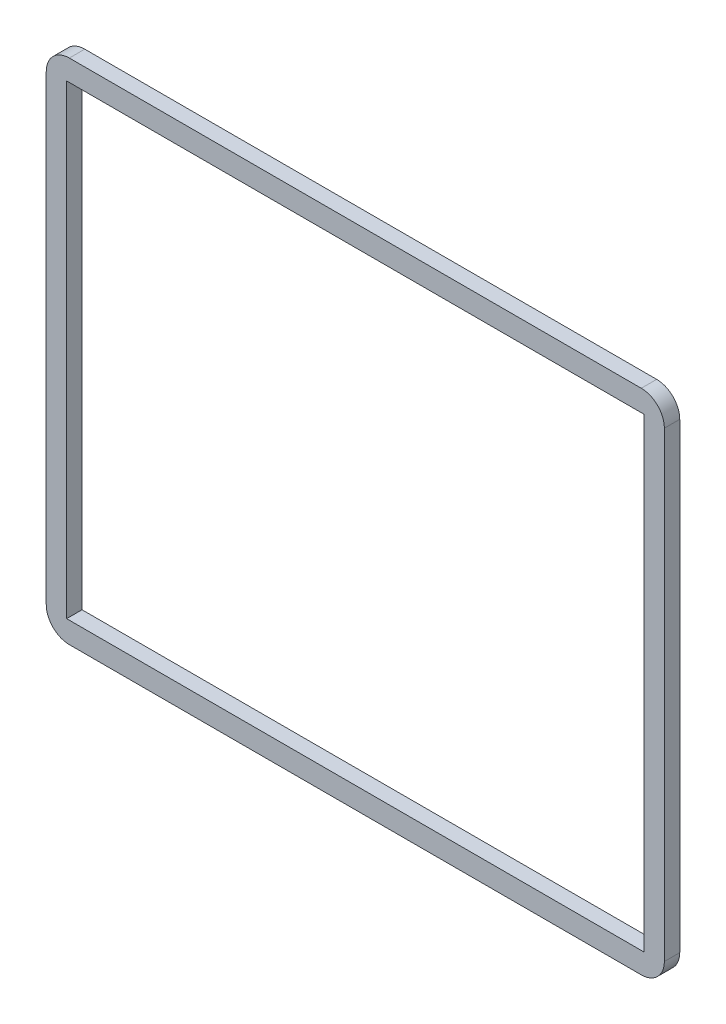
SolidWorks part; units mm, degrees
material "Acrylic (Medium-high impact)"
ref_plane "Front Plane" through (0, 0, 0) normal (0, 0, 1) x (1, 0, 0)
ref_plane "Top Plane" through (0, 0, 0) normal (0, 1, 0) x (1, 0, 0)
ref_plane "Right Plane" through (0, 0, 0) normal (1, 0, 0) x (0, 0, -1)
sketch "Sketch1" plane through (0, 0, 0) normal (0, 0, 1) x (1, 0, 0)
  line L1 (0, 0) -> (80.3, 0)
  line L2 (0, 0) -> (0, 66)
  line L3 (0, 66) -> (80.3, 66)
  line L4 (80.3, 0) -> (80.3, 66)
  dimension "D1" = 80.3
  dimension "D2" = 66
extrude "Boss-Extrude1" add sketch "Sketch1" along normal blind 2
hole_wizard "Ø3.2 (3.2) Diameter Hole1" positions "Sketch3" profile "Sketch2" hole size "Ø3.2" standard "ANSI Metric" end condition through all
sketch "Sketch3" plane through (0, 0, 2) normal (0, 0, 1) x (1, 0, 0)
  line L0 (0, 33) -> (80.3, 33) construction
  line L1 (0, 66) -> (0, 0) construction
  line L2 (80.3, 0) -> (80.3, 66) construction
  line L4 (7, 7) -> (7, 59) construction
  line L6 (7, 59) -> (73.3, 59) construction
  line L7 (73.3, 59) -> (73.3, 7) construction
  line L8 (73.3, 7) -> (7, 7) construction
  line L10 (40.15, 66) -> (40.15, 0) construction
  line L11 (80.3, 66) -> (0, 66) construction
  line L12 (0, 0) -> (80.3, 0) construction
  point P0 (7, 59)
  point P2 (73.3, 59)
  point P4 (73.3, 7)
  point P6 (7, 7)
  dimension "D1" = 66.3
  dimension "D2" = 52
  dimension "D3" = 26
  dimension "D4" = 33.15
sketch "Sketch2" plane through (7, 59, 2) normal (1, 0, 0) x (0, -1, 0)
  line L0 (0, 0) -> (0, 2)
  line L1 (0, 2) -> (1.6, 2)
  line L2 (1.6, 2) -> (1.6, 0)
  line L5 (1.6, 0) -> (0, 0)
  line L11 (0, -6.35) -> (0, 107.95) construction
  dimension "Thru Hole Dia." = 3.2
  dimension "Thru Hole Depth" = 2
fillet "Fillet1" radius 3 4 edges at (80.3, 66, 1) (80.3, 0, 1) (0, 0, 1) (0, 66, 1)
sketch "Sketch4" plane through (0, 0, 2) normal (0, 0, 1) x (1, 0, 0)
  line L0 (7, 59) -> (7, 7) construction
  line L1 (2.65, 2.75) -> (77.65, 2.75)
  line L2 (2.65, 2.75) -> (2.65, 63.25)
  line L3 (2.65, 63.25) -> (77.65, 63.25)
  line L4 (77.65, 2.75) -> (77.65, 63.25)
  line L5 (2.65, 33) -> (77.65, 33) construction
  line L6 (7, 59) -> (73.3, 59) construction
  line L7 (73.3, 59) -> (73.3, 7) construction
  line L8 (73.3, 7) -> (7, 7) construction
  line L9 (7, 33) -> (73.3, 33) construction
  line L10 (40.15, 59) -> (40.15, 7) construction
  line L11 (40.15, 63.25) -> (40.15, 2.75) construction
  dimension "D1" = 75
  dimension "D2" = 60.5
extrude "Cut-Extrude1" cut sketch "Sketch4" against normal through all
